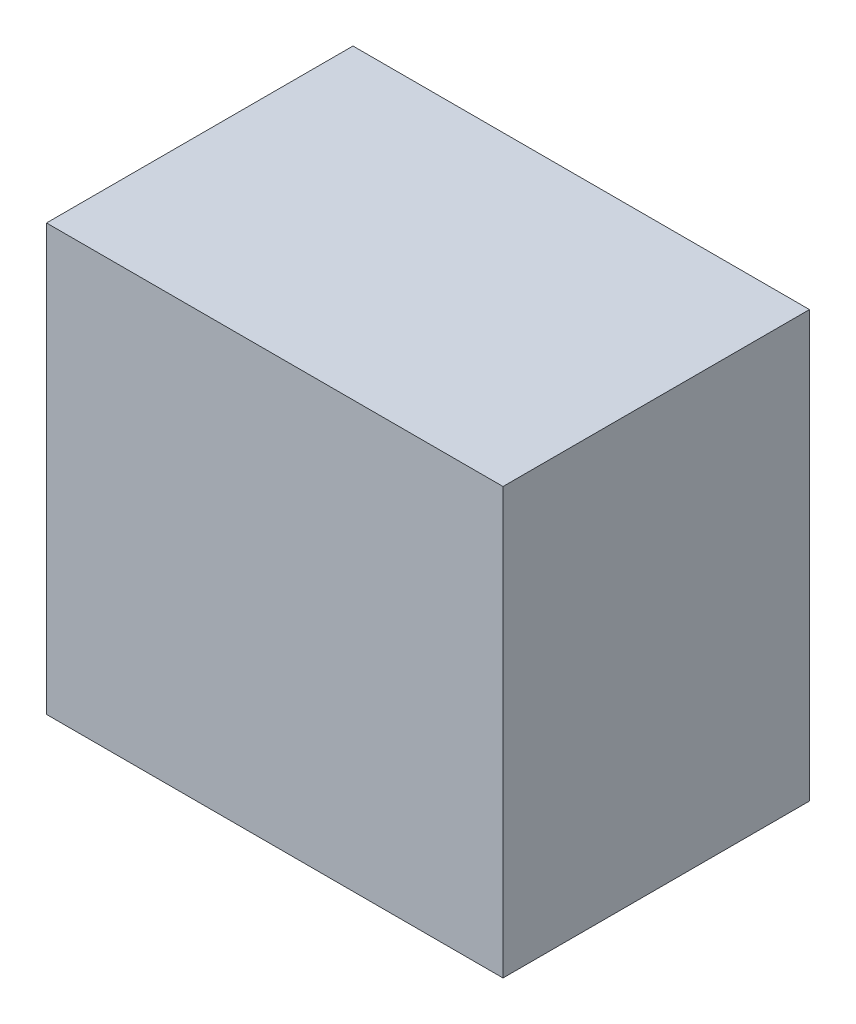
SolidWorks part; units mm, degrees
ref_plane "Front Plane" through (0, 0, 0) normal (0, 0, 1) x (1, 0, 0)
ref_plane "Top Plane" through (0, 0, 0) normal (0, 1, 0) x (1, 0, 0)
ref_plane "Right Plane" through (0, 0, 0) normal (1, 0, 0) x (0, 0, -1)
sketch "Sketch1" plane through (0, 0, 0) normal (0, 0, 1) x (1, 0, 0)
  line L1 (-30.1907, 22.6808) -> (12.7093, 22.6808)
  line L2 (-30.1907, 22.6808) -> (-30.1907, -17.3192)
  line L3 (-30.1907, -17.3192) -> (12.7093, -17.3192)
  line L4 (12.7093, 22.6808) -> (12.7093, -17.3192)
  dimension "D1" = 40
  dimension "D2" = 42.9
extrude "Boss-Extrude1" add sketch "Sketch1" along normal blind 28.8
